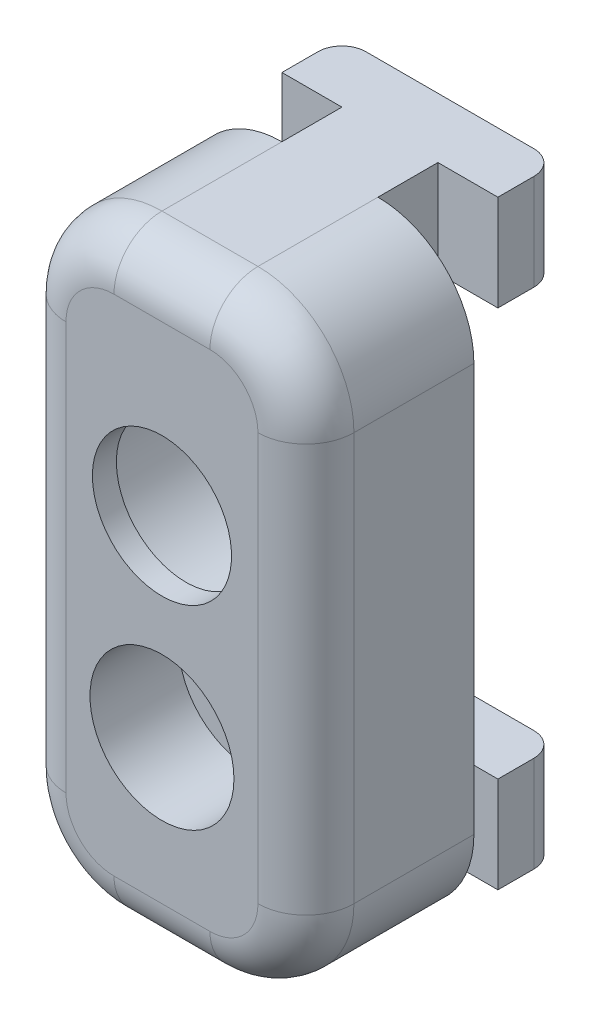
SolidWorks part; units mm, degrees
ref_plane "Plan de face" through (0, 0, 0) normal (0, 0, 1) x (1, 0, 0)
ref_plane "Plan de dessus" through (0, 0, 0) normal (0, 1, 0) x (1, 0, 0)
ref_plane "Plan de droite" through (0, 0, 0) normal (1, 0, 0) x (0, 0, -1)
sketch "Esquisse2" plane through (0, 0, 0) normal (0, 1, 0) x (1, 0, 0)
  line L1 (11.5687, 38.1282) -> (18.5687, 38.1282)
  line L2 (10.5687, 37.1282) -> (10.5687, 35.6282)
  line L3 (10.5687, 35.6282) -> (13.0687, 35.6282)
  line L4 (19.5687, 37.1282) -> (19.5687, 35.6282)
  line L7 (13.0687, 33.1282) -> (13.0687, 35.6282)
  line L9 (17.0687, 33.1282) -> (17.0687, 35.6282)
  line L10 (17.0687, 35.6282) -> (19.5687, 35.6282)
  line L11 (17.0687, 33.1282) -> (21.0687, 33.1282)
  line L12 (9.0687, 33.1282) -> (13.0687, 33.1282)
  line L13 (9.0687, 33.1282) -> (9.0687, 26.1282)
  line L14 (9.0687, 26.1282) -> (21.0687, 26.1282)
  line L15 (21.0687, 33.1282) -> (21.0687, 26.1282)
  arc A0 (18.5687, 38.1282) -> (19.5687, 37.1282) centre (18.5687, 37.1282) cw
  arc A1 (11.5687, 38.1282) -> (10.5687, 37.1282) centre (11.5687, 37.1282) ccw
  point P12 (15.0687, 38.1282)
  point P13 (15.0687, 26.1282)
  point P16 (19.5687, 38.1282)
  point P19 (10.5687, 38.1282)
  dimension "D4" = 1
  dimension "D1" = 9
  dimension "D2" = 2.5
  dimension "D3" = 4
  dimension "D5" = 2.5
  dimension "D6" = 12
  dimension "D7" = 7
extrude "Boss.-Extru.3" add sketch "Esquisse2" along normal blind 4
sketch "Esquisse3" plane through (0, 4, 0) normal (0, 1, 0) x (1, 0, 0)
  line L1 (9.0687, 33.1282) -> (21.0687, 33.1282)
  line L2 (9.0687, 33.1282) -> (9.0687, 26.1282)
  line L3 (9.0687, 26.1282) -> (21.0687, 26.1282)
  line L4 (21.0687, 33.1282) -> (21.0687, 26.1282)
extrude "Boss.-Extru.4" add sketch "Esquisse3" along normal blind 8.5
mirror "Symétrie1" about plane through (0, 12.5, 0) normal (0, 1, 0) of bodies 104
sketch "Esquisse4" plane through (0, 0, -33.1282) normal (0, 0, -1) x (-1, 0, 0)
  line L0 (-15.0687, 25) -> (-15.0687, 0) construction
  line L1 (-18.5687, 25) -> (-11.5687, 25) construction
  line L2 (-18.5687, 0) -> (-11.5687, 0) construction
  line L3 (-18.5687, 4) -> (-11.5687, 4) construction
  line L4 (-18.5687, 21) -> (-11.5687, 21) construction
  circle A1 centre (-15.0687, 8) radius 1.65
  circle A2 centre (-15.0687, 16) radius 2.9
  dimension "D1" = 3.3
  dimension "D3" = 5.8
  dimension "D2" = 4
  dimension "D4" = 5
extrude "Enlèv. mat.-Extru.1" cut sketch "Esquisse4" against normal up to next
sketch "Esquisse5" plane through (0, 0, -33.1282) normal (0, 0, -1) x (-1, 0, 0)
  line L13 (-18.5687, 21) -> (-11.5687, 21) construction
  line L14 (-15.0687, 25) -> (-15.0687, 0) construction
  line L15 (-18.5687, 25) -> (-11.5687, 25) construction
  line L16 (-18.5687, 0) -> (-11.5687, 0) construction
  circle A0 centre (-15.0687, 16) radius 4.1
  dimension "D1" = 8.2
  dimension "D2" = 5
extrude "Enlèv. mat.-Extru.2" cut sketch "Esquisse5" against normal blind 6
fillet "Congé1" radius 4 4 edges at (9.0687, 0, -29.6282) (9.0687, 25, -29.6282) (21.0687, 0, -29.6282) (21.0687, 25, -29.6282)
fillet "Congé2" radius 2 8 edges at (21.0687, 12.5, -26.1282) (19.8972, 1.1716, -26.1282) (15.0687, 0, -26.1282) (10.2403, 1.1716, -26.1282) (9.0687, 12.5, -26.1282) (10.2403, 23.8284, -26.1282) (15.0687, 25, -26.1282) (19.8972, 23.8284, -26.1282)
sketch "Esquisse6" plane through (0, 0, -26.1282) normal (0, 0, 1) x (1, 0, 0)
  circle A0 centre (15.0687, 8) radius 3
  dimension "D1" = 6
extrude "Enlèv. mat.-Extru.3" cut sketch "Esquisse6" against normal blind 3.7
sketch "Esquisse7" plane through (0, 0, -33.1282) normal (0, 0, -1) x (-1, 0, 0)
  line L0 (-16.7142, 10.85) -> (-13.4233, 10.85)
  line L1 (-13.4233, 10.85) -> (-11.7778, 8)
  line L2 (-11.7778, 8) -> (-13.4233, 5.15)
  line L3 (-13.4233, 5.15) -> (-16.7142, 5.15)
  line L4 (-16.7142, 5.15) -> (-18.3596, 8)
  line L5 (-18.3596, 8) -> (-16.7142, 10.85)
  line L6 (-16.7142, 10.85) -> (-13.4233, 5.15) construction
  point P4 (-15.0687, 8)
  point P7 (-15.0687, 8)
  dimension "D1" = 5.7
  dimension "D2" = 120
  dimension "D3" = 5.7
extrude "Enlèv. mat.-Extru.4" cut sketch "Esquisse7" against normal blind 2
